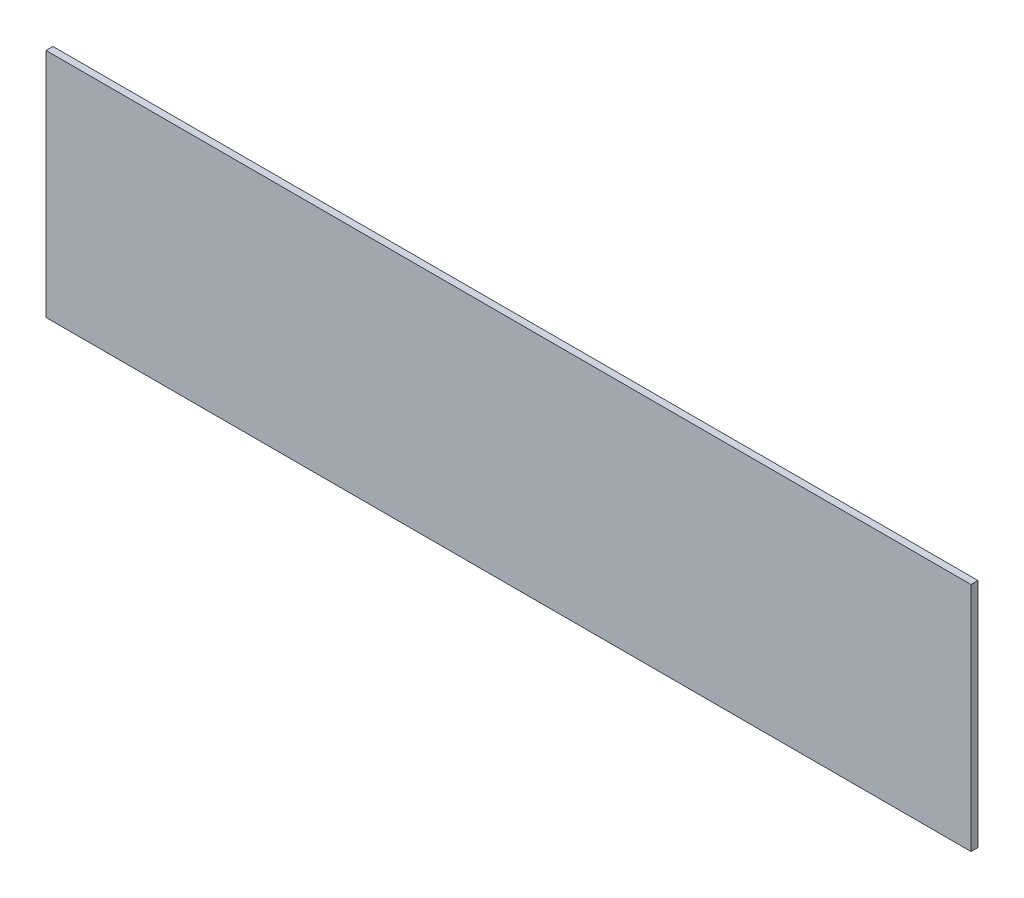
SolidWorks part; units mm, degrees
ref_plane "Front Plane" through (0, 0, 0) normal (0, 0, 1) x (1, 0, 0)
ref_plane "Top Plane" through (0, 0, 0) normal (0, 1, 0) x (1, 0, 0)
ref_plane "Right Plane" through (0, 0, 0) normal (1, 0, 0) x (0, 0, -1)
sketch "Sketch1" plane through (0, 0, 0) normal (0, 0, 1) x (1, 0, 0)
  line L1 (0, 0) -> (408, 0)
  line L2 (0, 0) -> (0, 100)
  line L3 (0, 100) -> (408, 100)
  line L4 (408, 0) -> (408, 100)
  dimension "D1" = 408
  dimension "D2" = 100
extrude "Boss-Extrude1" add sketch "Sketch1" along normal blind 3
sketch "Sketch3" plane through (0, 0, 0) normal (0, 0, -1) x (-1, 0, 0)
  line L0 (0, 0) -> (-408, 0) construction
  line L1 (0, 100) -> (-8, 100)
  line L2 (0, 100) -> (0, 0)
  line L3 (0, 0) -> (-8, 0)
  line L4 (-8, 100) -> (-8, 0)
  dimension "D1" = 8
extrude "Cut-Extrude2" cut sketch "Sketch3" against normal blind 10
